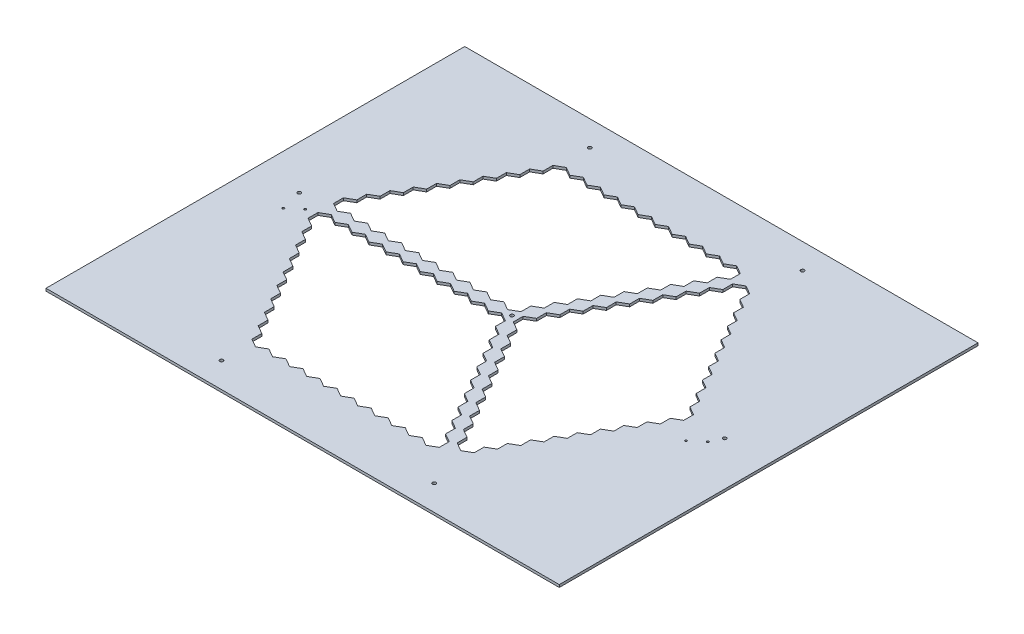
SolidWorks part; units mm, degrees
material "Acrylic (Medium-high impact)"
ref_plane "Front Plane" through (0, 0, 0) normal (0, 0, 1) x (1, 0, 0)
ref_plane "Top Plane" through (0, 0, 0) normal (0, 1, 0) x (1, 0, 0)
ref_plane "Right Plane" through (0, 0, 0) normal (1, 0, 0) x (0, 0, -1)
sketch "Sketch1" plane through (0, 0, 0) normal (0, 1, 0) x (1, 0, 0)
  line L11 (-482.6, 393.7) -> (482.6, 393.7)
  line L12 (-482.6, 393.7) -> (-482.6, -393.7)
  line L13 (-482.6, -393.7) -> (482.6, -393.7)
  line L14 (482.6, 393.7) -> (482.6, -393.7)
  point P0 (0, 393.7)
  point P2 (-482.6, 0)
  dimension "D1" = 787.4
  dimension "D2" = 965.2
extrude "Base" add sketch "Sketch1" along normal blind 4.7625
sketch "Border Sketch" plane through (0, 4.7625, 0) normal (0, 1, 0) x (1, 0, 0)
  line L7 (450, 0) -> (225, 389.7114)
  line L8 (225, 389.7114) -> (-225, 389.7114)
  line L9 (-225, 389.7114) -> (-450, 0)
  line L10 (-450, 0) -> (-225, -389.7114)
  line L11 (-225, -389.7114) -> (225, -389.7114)
  line L12 (225, -389.7114) -> (450, 0)
  line L14 (225, 389.7114) -> (0, 0)
  line L15 (0, 0) -> (225, -389.7114)
  line L20 (-450, 0) -> (0, 0)
  line L21 (0, 5.5) -> (-446.8246, 5.5)
  line L22 (0, -5.5) -> (-446.8246, -5.5)
  line L23 (218.6491, 389.7114) -> (-4.7631, 2.75)
  line L24 (4.7631, -2.75) -> (228.1754, 384.2114)
  line L25 (4.7631, 2.75) -> (228.1754, -384.2114)
  line L26 (-4.7631, -2.75) -> (218.6491, -389.7114)
  circle A0 centre (0, 0) radius 450 construction
  circle A1 centre (0, 0) radius 5.5
  dimension "D1" = 5.5
  dimension "D2" = 5.5
  dimension "D3" = 5.5
  dimension "D4" = 5.5
sketch "Sketch3" plane through (0, 4.7625, 0) normal (0, 1, 0) x (1, 0, 0)
  line L8 (-13.8564, -5.5) -> (-29.8779, -14.75)
  line L9 (-29.8779, -14.75) -> (-29.8779, -33.25)
  line L10 (-29.8779, -33.25) -> (-13.8564, -42.5)
  line L11 (-13.8564, -42.5) -> (2.1651, -33.25)
  line L12 (2.1651, -33.25) -> (2.1651, -14.75)
  line L13 (2.1651, -14.75) -> (-13.8564, -5.5)
  line L15 (0, -5.5) -> (-446.8246, -5.5) construction
  line L16 (-4.7631, -2.75) -> (218.6491, -389.7114) construction
  circle A0 centre (-13.8564, -24) radius 18.5 construction
extrude "Bottom Dish Cut" cut sketch "Sketch3" against normal up to next
pattern_linear "Bottom Dish Pattern" count 11 spacing 32.04 along (-1, 0, 0) count 10 spacing 32.04 along (0.5, 0, 0.866) of "Bottom Dish Cut"
sketch "Sketch4" plane through (0, 4.7625, 0) normal (0, 1, 0) x (1, 0, 0)
  line L1 (-13.8564, 42.5) -> (-29.8779, 33.25)
  line L2 (-29.8779, 33.25) -> (-29.8779, 14.75)
  line L3 (-29.8779, 14.75) -> (-13.8564, 5.5)
  line L4 (-13.8564, 5.5) -> (2.1651, 14.75)
  line L5 (2.1651, 14.75) -> (2.1651, 33.25)
  line L6 (2.1651, 33.25) -> (-13.8564, 42.5)
  line L8 (0, 5.5) -> (-446.8246, 5.5) construction
  line L9 (218.6491, 389.7114) -> (-4.7631, 2.75) construction
  circle A0 centre (-13.8564, 24) radius 18.5 construction
extrude "Top Dish Cut" cut sketch "Sketch4" against normal up to next
pattern_linear "Top Dish Pattern" count 11 spacing 32.04 along (-1, 0, 0) count 10 spacing 32.04 along (0.5, 0, -0.866) of "Top Dish Cut"
sketch "Sketch5" plane through (0, 4.7625, 0) normal (0, 1, 0) x (1, 0, 0)
  line L1 (27.7128, 18.5) -> (11.6913, 9.25)
  line L2 (11.6913, 9.25) -> (11.6913, -9.25)
  line L3 (11.6913, -9.25) -> (27.7128, -18.5)
  line L4 (27.7128, -18.5) -> (43.7343, -9.25)
  line L5 (43.7343, -9.25) -> (43.7343, 9.25)
  line L6 (43.7343, 9.25) -> (27.7128, 18.5)
  line L8 (4.7631, 2.75) -> (228.1754, -384.2114) construction
  line L9 (4.7631, -2.75) -> (228.1754, 384.2114) construction
  circle A0 centre (27.7128, 0) radius 18.5 construction
extrude "Right Dish Cut" cut sketch "Sketch5" against normal up to next
pattern_linear "Right Dish Pattern" count 10 spacing 32.04 along (0.5, 0, -0.866) count 10 spacing 32.04 along (0.5, 0, 0.866) of "Right Dish Cut"
hole_wizard "Ø6.5 (6.5) Diameter Hole1" positions "Sketch6" profile "Sketch7" hole size "Ø6.5" standard "ANSI Metric"
sketch "Sketch6" plane through (0, 4.7625, 0) normal (0, 1, 0) x (1, 0, 0)
  point P0 (0, 0)
  point P3 (-400, 0)
  point P11 (-200, 346.4102)
  point P12 (200, 346.4102)
  point P13 (400, 0)
  point P14 (200, -346.4102)
  point P15 (-200, -346.4102)
  point P16 (0, 0)
sketch "Sketch7" plane through (0, 4.7625, 0) normal (1, 0, 0) x (0, 0, 1)
  line L0 (0, 0) -> (0, 4.7625)
  line L1 (0, 4.7625) -> (3.25, 4.7625)
  line L2 (3.25, 4.7625) -> (3.25, 0)
  line L3 (3.25, 0) -> (0, 0)
  line L4 (0, -6.35) -> (0, 107.95) construction
  dimension "Thru Hole Dia." = 6.5
  dimension "Thru Hole Depth" = 4.7625
hole_wizard "Ø4.0 (4) Diameter Hole1" positions "Sketch8" profile "Sketch9" hole size "Ø4.0" standard "ANSI Metric"
sketch "Sketch8" plane through (0, -9.525, 0) normal (0, -1, 0) x (-1, 0, 0)
  point P0 (-389.7627, -21.2724)
  point P3 (-367.5377, -40.3224)
  point P6 (367.5377, -21.2724)
  point P9 (389.7627, -40.3224)
sketch "Sketch9" plane through (389.7627, -9.525, 21.2724) normal (1, 0, 0) x (0, 0, -1)
  line L0 (0, 0) -> (0, 14.2875)
  line L1 (0, 14.2875) -> (2, 14.2875)
  line L2 (2, 14.2875) -> (2, 0)
  line L3 (2, 0) -> (0, 0)
  line L4 (0, -6.35) -> (0, 107.95) construction
  dimension "Thru Hole Dia." = 4
  dimension "Thru Hole Depth" = 14.2875
sketch "Sketch10" plane through (0, 4.7625, 0) normal (0, 1, 0) x (1, 0, 0)
  line L0 (270.6976, 347.0172) -> (473.8976, 347.0172)
  line L1 (433.0127, 0) -> (216.5064, 375)
  line L2 (216.5064, 375) -> (-216.5064, 375)
  line L3 (-216.5064, 375) -> (-433.0127, 0)
  line L4 (-433.0127, 0) -> (-216.5064, -375)
  line L5 (-216.5064, -375) -> (216.5064, -375)
  line L6 (216.5064, -375) -> (433.0127, 0)
  line L7 (-471.0934, 351.6961) -> (-267.8934, 351.6961)
  line L8 (-471.0934, 351.6961) -> (-471.0934, 300.8961)
  line L9 (-471.0934, 300.8961) -> (-267.8934, 300.8961)
  line L10 (-267.8934, 351.6961) -> (-267.8934, 300.8961)
  line L11 (270.6976, 347.0172) -> (270.6976, 296.2172)
  line L12 (270.6976, 296.2172) -> (473.8976, 296.2172)
  line L13 (473.8976, 347.0172) -> (473.8976, 296.2172)
  line L14 (267.1706, -302.8303) -> (470.3706, -302.8303)
  line L15 (267.1706, -302.8303) -> (267.1706, -353.6303)
  line L16 (267.1706, -353.6303) -> (470.3706, -353.6303)
  line L17 (470.3706, -302.8303) -> (470.3706, -353.6303)
  line L18 (-475.7012, -284.3136) -> (-272.5012, -284.3136)
  line L19 (-475.7012, -284.3136) -> (-475.7012, -335.1136)
  line L20 (-475.7012, -335.1136) -> (-272.5012, -335.1136)
  line L21 (-272.5012, -284.3136) -> (-272.5012, -335.1136)
  dimension "D1" = 50.8
  dimension "D2" = 203.2
